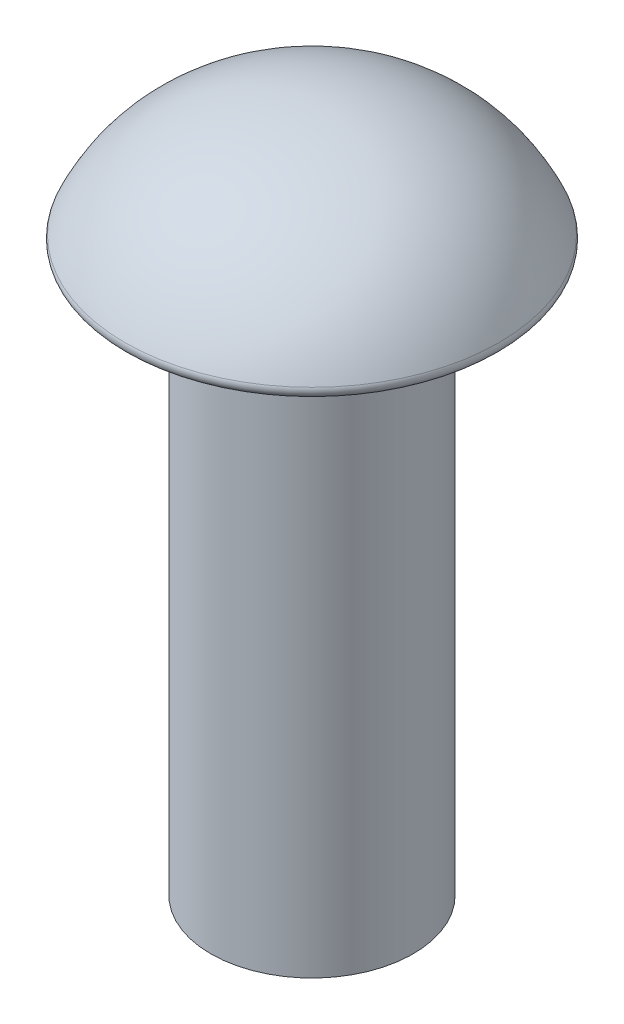
SolidWorks part; units mm, degrees
ref_plane "Front Plane" through (0, 0, 0) normal (0, 0, 1) x (1, 0, 0)
ref_plane "Top Plane" through (0, 0, 0) normal (0, 1, 0) x (1, 0, 0)
ref_plane "Right Plane" through (0, 0, 0) normal (1, 0, 0) x (0, 0, -1)
sketch "Sketch1" plane through (0, 0, 0) normal (0, 1, 0) x (1, 0, 0)
  circle A0 centre (0, 0) radius 2.4
  dimension "D1" = 4.8
extrude "Boss-Extrude1" add sketch "Sketch1" along normal blind 13.3
sketch "Sketch2" plane through (0, 0, 0) normal (0, 0, 1) x (1, 0, 0)
  line L0 (0, 13.3) -> (0, 16.2) construction
  line L1 (2.4, 13.3) -> (-2.4, 13.3) construction
  line L2 (0, 13.3) -> (-4.55, 13.3) construction
  line L3 (0, 16.2) -> (1.2411, 16.2) construction
  line L4 (-4.55, 13.3) -> (0, 13.3)
  line L5 (0, 13.3) -> (0, 16.2)
  spline S0 degree 3 poles (0, 16.2) (-1.7985, 16.2) (-3.7165, 15.4373) (-4.55, 13.3) knots 0 0 0 0 1 1 1 1
  dimension "D1" = 4.55
  dimension "D2" = 2.9
revolve "Revolve1" add sketch "Sketch2" angle 360 about L5
fillet "Fillet1" radius 0.1905 1 edges at (0, 13.3, -4.55)
